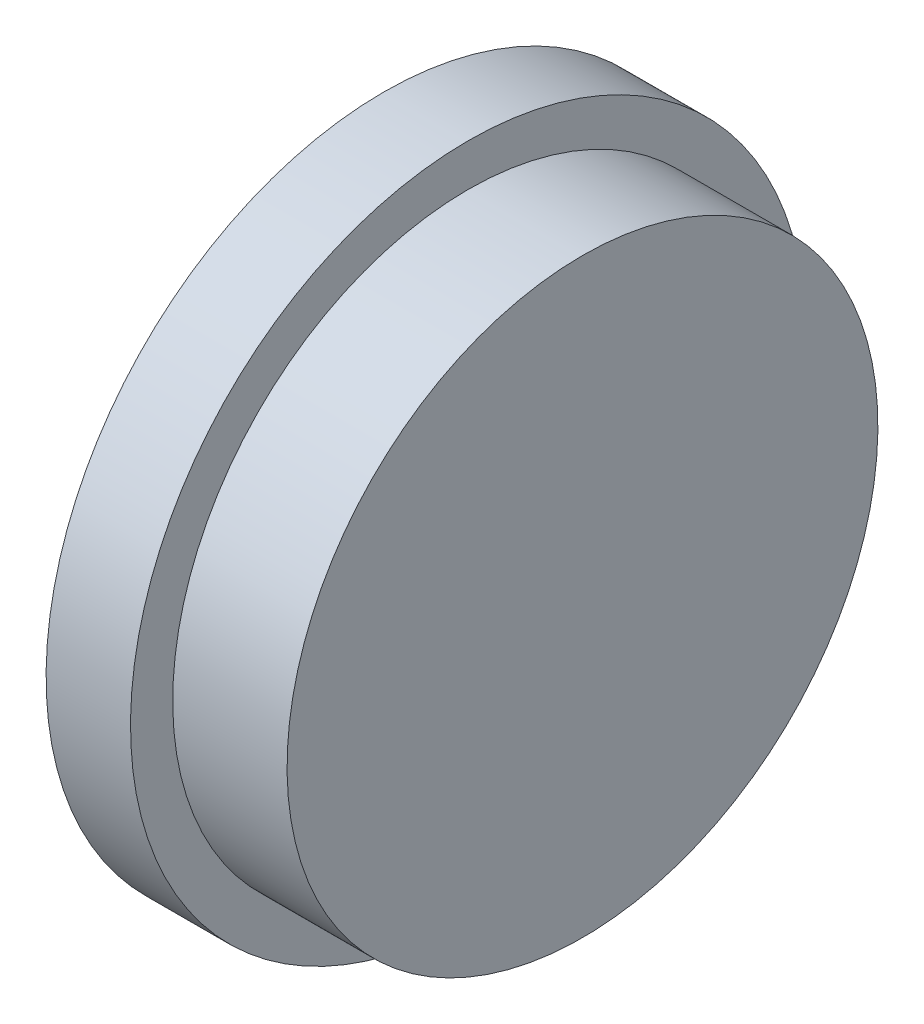
SolidWorks part; units mm, degrees
ref_plane "Plan de face" through (0, 0, 0) normal (0, 0, 1) x (1, 0, 0)
ref_plane "Plan de dessus" through (0, 0, 0) normal (0, 1, 0) x (1, 0, 0)
ref_plane "Plan de droite" through (0, 0, 0) normal (1, 0, 0) x (0, 0, -1)
sketch "Esquisse1" plane through (0, 0, 0) normal (0, 0, 1) x (1, 0, 0)
  line L0 (0.871, 24) -> (6.871, 24)
  line L1 (6.871, 24) -> (6.871, 21)
  line L2 (6.871, 21) -> (15, 21)
  line L3 (15, 21) -> (15, 0)
  line L4 (15, 0) -> (13, 0)
  line L5 (13, 0) -> (13, 16)
  line L6 (13, 16) -> (0.871, 16)
  line L7 (0.871, 16) -> (0.871, 24)
  line L8 (13, 0) -> (0, 0) construction
  point P2 (0, 0)
  point P11 (0, 0)
  dimension "D1" = 2
  dimension "D2" = 21
  dimension "D3" = 8
  dimension "D4" = 6
  dimension "D5" = 15
  dimension "D6" = 16
revolve "Révolution1" add sketch "Esquisse1" angle 360 about L8
sketch "Esquisse2" plane through (0, 0, 0) normal (1, 0, 0) x (0, 0, -1)
  line L0 (-14.6328, 0) -> (18.3672, 0)
  line L1 (18.3672, 0) -> (18.3672, -2)
  line L2 (18.3672, -2) -> (-14.6328, -2)
  line L3 (-14.6328, -2) -> (-14.6328, 0)
  line L4 (0, 0) -> (0, -23) construction
  dimension "D1" = 33
  dimension "D2" = 2
  dimension "D3" = 21
